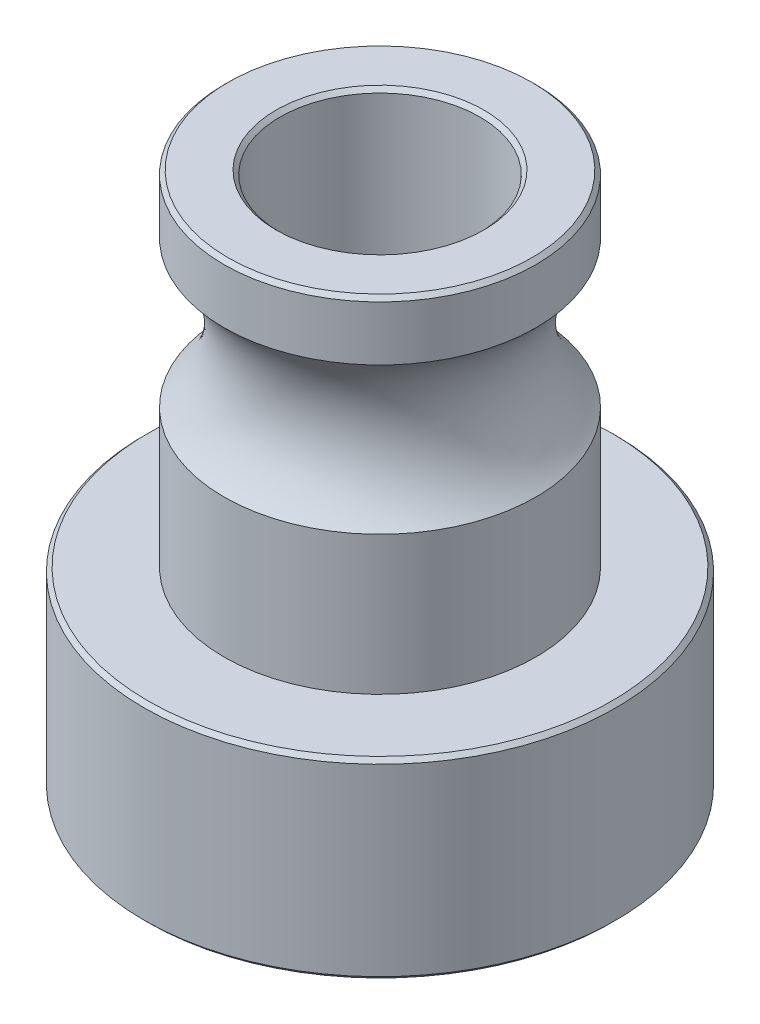
SolidWorks part; units mm, degrees
ref_plane "Alzado" through (0, 0, 0) normal (0, 0, 1) x (1, 0, 0)
ref_plane "Planta" through (0, 0, 0) normal (0, 1, 0) x (1, 0, 0)
ref_plane "Vista lateral" through (0, 0, 0) normal (1, 0, 0) x (0, 0, -1)
sketch "Croquis1" plane through (0, 0, 0) normal (0, 1, 0) x (1, 0, 0)
  circle A0 centre (0, 0) radius 5.9
  dimension "D1" = 11.8
extrude "Saliente-Extruir1" add sketch "Croquis1" along normal blind 4.8
sketch "Croquis2" plane through (0, 0, 0) normal (0, 1, 0) x (1, 0, 0)
  circle A0 centre (0, 0) radius 3.9
  dimension "D1" = 7.8
extrude "Saliente-Extruir2" add sketch "Croquis2" along normal blind 13.4
sketch "Croquis3" plane through (0, 13.4, 0) normal (0, 1, 0) x (1, 0, 0)
  circle A0 centre (0, 0) radius 2.5
  dimension "D1" = 5
extrude "Cortar-Extruir1" cut sketch "Croquis3" against normal through all
chamfer "Chaflán1" distance 0.1 angle 45 5 edges at (0, 0, 2.5) (0, 0, 5.9) (0, 4.8, 5.9) (0, 13.4, 2.5) (0, 13.4, 3.9)
sketch "Croquis4" plane through (0, 0, 0) normal (1, 0, 0) x (0, 0, -1)
  line L0 (2.6, 13.4) -> (-2.6, 13.4) construction
  line L2 (0, 13.9795) -> (0, -0.3939) construction
  line L3 (0, 6.49) -> (0, -6.49) construction
  circle A0 centre (-5.6, 10.1) radius 2.5
  dimension "D2" = 5
  dimension "D1" = 3.3
revolve "Cortar-Revolución2" cut sketch "Croquis4" angle 360 about L2
sketch "Croquis5" plane through (0, 0, 0) normal (0, 0, 1) x (1, 0, 0)
  line L0 (0, -6.49) -> (0, 6.49) construction
  line L1 (6.49, 0) -> (-6.49, 0) construction
  circle A0 centre (0, 2.4) radius 1.5
  dimension "D1" = 3
  dimension "D2" = 2.4
extrude "Cortar-Extruir2" cut sketch "Croquis5" against normal through all
